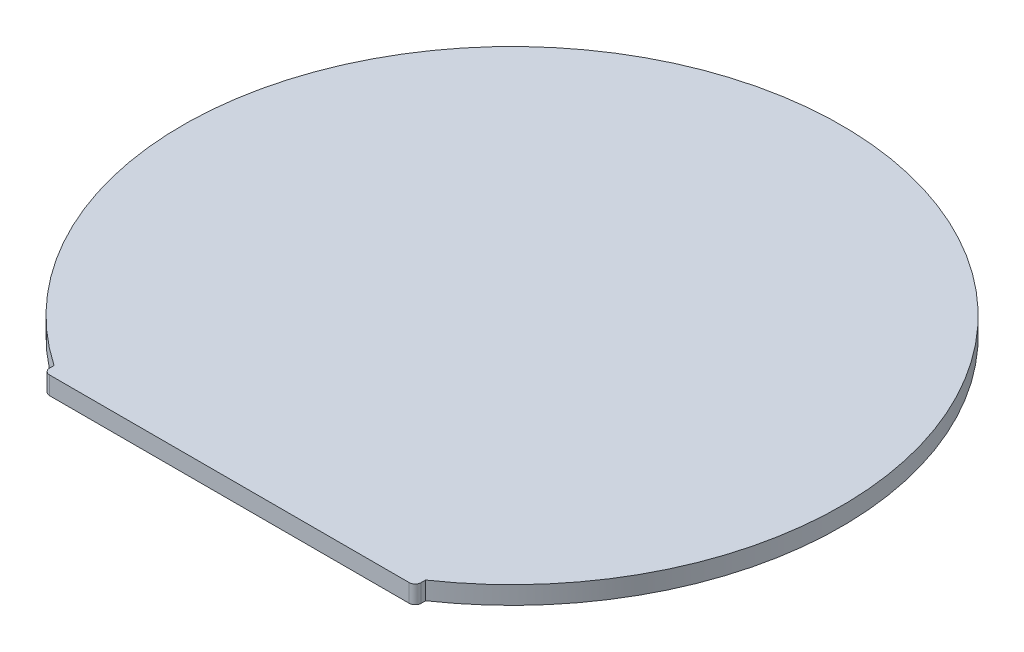
SolidWorks part; units mm, degrees
material "A-Glass Fiber"
ref_plane "Front Plane" through (0, 0, 0) normal (0, 0, 1) x (1, 0, 0)
ref_plane "Top Plane" through (0, 0, 0) normal (0, 1, 0) x (1, 0, 0)
ref_plane "Right Plane" through (0, 0, 0) normal (1, 0, 0) x (0, 0, -1)
sketch "Sketch1" plane through (0, 0, 0) normal (0, 1, 0) x (1, 0, 0)
  line L2 (-15.5, -23.585) -> (16, -23.585) construction
  line L3 (-15.5, -23.585) -> (15.5, -23.585)
  line L4 (-15.5, -23.585) -> (-15.5, -22.7156)
  line L5 (15.5, -23.585) -> (15.5, -22.7156)
  line L6 (-16, -23.585) -> (-15.5, -23.585) construction
  circle A2 centre (0, 0) radius 28.5 construction
  arc A4 (15.5, -22.7156) -> (-15.5, -22.7156) centre (0, 0) ccw
  arc A5 (-15.5, -22.7156) -> (-14.1421, -23.585) centre (0, 0) ccw construction
  arc A6 (-14.1421, -23.585) -> (14.1421, -23.585) centre (0, 0) ccw construction
  arc A7 (14.1421, -23.585) -> (15.5, -22.7156) centre (0, 0) ccw construction
  point P8 (0, -23.585)
  dimension "D1" = 55
  dimension "D3" = 57
  dimension "D4" = 31
  dimension "D2" = 32
extrude "Boss-Extrude1" add sketch "Sketch1" along normal blind 1.5
fillet "Fillet1" radius 0.5 2 edges at (15.5, 0.75, 23.585) (-15.5, 0.75, 23.585)
